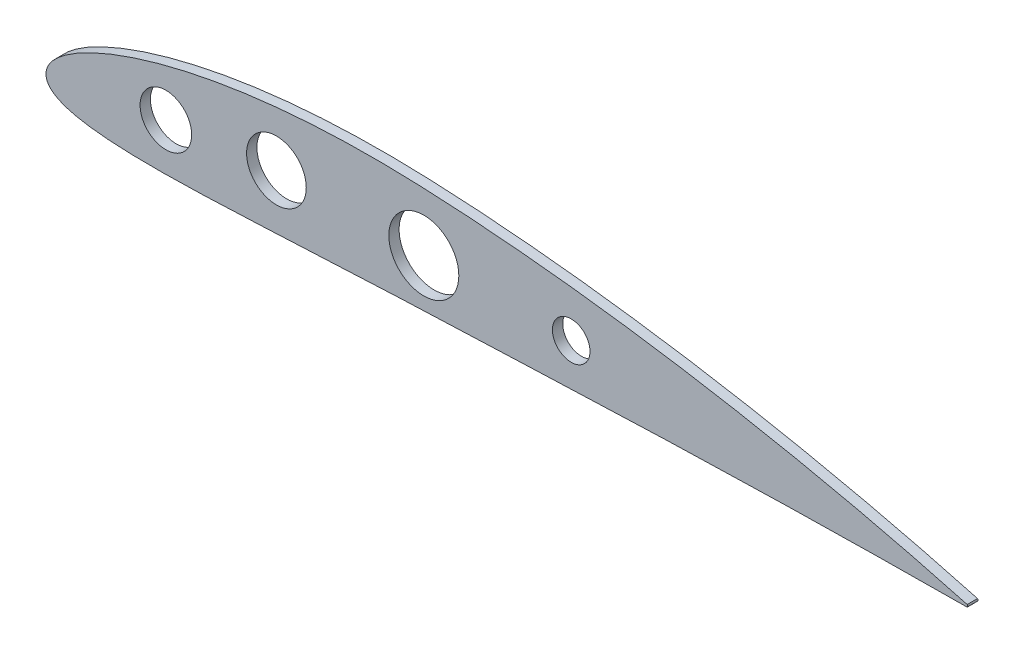
SolidWorks part; units mm, degrees
material "Фанера"
ref_plane "Front Plane" through (0, 0, 0) normal (0, 0, 1) x (1, 0, 0)
ref_plane "Top Plane" through (0, 0, 0) normal (0, 1, 0) x (1, 0, 0)
ref_plane "Right Plane" through (0, 0, 0) normal (1, 0, 0) x (0, 0, -1)
curve "Кривая5"
  spline degree 3 poles (0.048, 0.6214, 0) (0.0227, 0.3735, 0) (-0.0278, -0.1225, 0) (0.078, -0.8844, 0) (0.3497, -1.6388, 0) (0.8143, -2.3651, 0) (1.4635, -3.0393, 0) (2.291, -3.661, 0) (3.3059, -4.2358, 0) (4.5353, -4.7737, 0) (6.0297, -5.2822, 0) (7.869, -5.7653, 0) (10.1688, -6.2217, 0) (13.0754, -6.6396, 0) (16.7281, -6.993, 0) (21.19, -7.2473, 0) (26.4, -7.3766, 0) (32.1974, -7.3763, 0) (38.3978, -7.2614, 0) (44.8576, -7.0566, 0) (51.4865, -6.7865, 0) (58.231, -6.4723, 0) (65.0521, -6.1329, 0) (71.9108, -5.784, 0) (78.7714, -5.4397, 0) (85.6105, -5.111, 0) (92.4321, -4.805, 0) (99.255, -4.532, 0) (106.0974, -4.2783, 0) (112.9692, -4.0031, 0) (119.8644, -3.7232, 0) (126.7739, -3.4401, 0) (133.6816, -3.1587, 0) (140.5819, -2.8824, 0) (147.472, -2.6139, 0) (154.3526, -2.3556, 0) (161.225, -2.1094, 0) (168.0909, -1.8766, 0) (174.9516, -1.6586, 0) (181.8086, -1.4564, 0) (188.6632, -1.2704, 0) (195.5166, -1.1011, 0) (202.3695, -0.9486, 0) (209.2212, -0.8129, 0) (216.0668, -0.6936, 0) (222.8864, -0.5903, 0) (229.6176, -0.5029, 0) (236.0874, -0.4315, 0) (241.9808, -0.3765, 0) (246.559, -0.3395, 0) (249.1205, -0.3213, 0) (250, -0.315, 0) knots 0 0 0 0 0.002941 0.005884 0.009016 0.012365 0.016008 0.020037 0.024574 0.029784 0.035897 0.04324 0.052276 0.063635 0.077983 0.095698 0.11652 0.139661 0.164312 0.189919 0.216157 0.242838 0.269834 0.296993 0.324123 0.351139 0.378036 0.404946 0.431961 0.459078 0.486347 0.513641 0.540929 0.568176 0.59538 0.622543 0.649673 0.676775 0.703855 0.730919 0.757971 0.785018 0.812062 0.839103 0.866132 0.893099 0.919831 0.94581 0.969681 0.98959 1 1 1 1
curve "Кривая6"
  spline degree 3 poles (250, 0.315, 0) (249.1557, 0.545, 0) (246.7202, 1.2085, 0) (242.3913, 2.3583, 0) (236.8498, 3.7876, 0) (230.7799, 5.298, 0) (224.4559, 6.8129, 0) (218.0305, 8.2916, 0) (211.5624, 9.7197, 0) (205.0724, 11.0924, 0) (198.568, 12.4079, 0) (192.0524, 13.6653, 0) (185.5276, 14.8641, 0) (178.9953, 16.0034, 0) (172.4571, 17.0824, 0) (165.9143, 18.0998, 0) (159.3687, 19.0545, 0) (152.8218, 19.9449, 0) (146.2754, 20.7693, 0) (139.7314, 21.5257, 0) (133.1918, 22.212, 0) (126.6587, 22.8257, 0) (120.1368, 23.364, 0) (113.6286, 23.8247, 0) (107.1527, 24.2002, 0) (100.7411, 24.4984, 0) (94.4118, 24.6866, 0) (88.1559, 24.7401, 0) (81.949, 24.6588, 0) (75.7805, 24.441, 0) (69.6537, 24.0819, 0) (63.5754, 23.578, 0) (57.5552, 22.9249, 0) (51.6058, 22.1191, 0) (45.7444, 21.1566, 0) (39.9959, 20.0354, 0) (34.3979, 18.7563, 0) (29.0104, 17.3276, 0) (23.9258, 15.7719, 0) (19.2707, 14.1343, 0) (15.1791, 12.4833, 0) (11.7405, 10.8956, 0) (8.9594, 9.4296, 0) (6.7609, 8.1086, 0) (5.0337, 6.9246, 0) (3.6717, 5.8542, 0) (2.5921, 4.8713, 0) (1.7382, 3.9526, 0) (1.0699, 3.0809, 0) (0.5716, 2.2416, 0) (0.2158, 1.4308, 0) (0.1023, 0.8832, 0) (0.048, 0.6214, 0) knots 0 0 0 0 0.010162 0.029313 0.052012 0.076619 0.101948 0.127526 0.153184 0.178868 0.204558 0.230246 0.255926 0.281594 0.307246 0.332878 0.358485 0.384061 0.409603 0.435104 0.460559 0.485959 0.511303 0.536552 0.561723 0.586629 0.611085 0.635251 0.659272 0.683164 0.706922 0.730536 0.753983 0.777235 0.800246 0.822951 0.845237 0.866916 0.887662 0.906968 0.924203 0.938879 0.950932 0.960693 0.968647 0.975233 0.980795 0.985584 0.989782 0.993521 0.996902 1 1 1 1
sketch "Эскиз1" plane through (0, 0, 0) normal (0, 0, 1) x (1, 0, 0)
  line L0 (250.1305, 0) -> (250.1305, 54.8427) construction
  line L1 (0, 0) -> (0, 70.5199) construction
  line L2 (0, 0) -> (253.0634, 0) construction
  line L3 (62.5326, 62.6361) -> (62.5326, -41.5636) construction
  line L4 (142.5326, 67.9319) -> (142.5326, -57.0034) construction
  line L5 (175.0913, 63.8571) -> (175.0913, -32.3947) construction
  line L6 (32.5326, -14.3434) -> (32.5326, 29.5903) construction
  arc A0 (250, 0.315) -> (250, -0.315) centre (249.685, 0) cw
  circle A1 centre (62.5326, 8.5962) radius 8.1
  circle A2 centre (142.5326, 8.5962) radius 5.1
  circle A3 centre (32.5326, 5.4481) radius 7
  circle A5 centre (102.5326, 8.5962) radius 9.5
  spline S0 degree 3 poles (-1998.9862, 52.2873) (51.3697, 19.9849) (-1.4299, 9.9734) (0.078, -0.8844) (0.3497, -1.6388) (0.8143, -2.3651) (1.4635, -3.0393) (2.291, -3.661) (3.3059, -4.2358) (4.5353, -4.7737) (6.0297, -5.2822) (7.869, -5.7653) (10.1688, -6.2217) (13.0754, -6.6396) (16.7281, -6.993) (21.19, -7.2473) (26.4, -7.3766) (32.1974, -7.3763) (38.3978, -7.2614) (44.8576, -7.0566) (51.4865, -6.7865) (58.231, -6.4723) (65.0521, -6.1329) (71.9108, -5.784) (78.7714, -5.4397) (85.6105, -5.111) (92.4321, -4.805) (99.255, -4.532) (106.0974, -4.2783) (112.9692, -4.0031) (119.8644, -3.7232) (126.7739, -3.4401) (133.6816, -3.1587) (140.5819, -2.8824) (147.472, -2.6139) (154.3526, -2.3556) (161.225, -2.1094) (168.0909, -1.8766) (174.9516, -1.6586) (181.8086, -1.4564) (188.6632, -1.2704) (195.5166, -1.1011) (202.3695, -0.9486) (211.4992, -0.7677) (220.6031, -0.6199) (229.6176, -0.5029) (236.0874, -0.4315) (241.9808, -0.3765) (412.2827, 0.9993) (580.6451, -8.1221) (733.0822, 1918.4656) knots -0.119467 -0.119467 -0.119467 -0.119467 0.002941 0.005884 0.009016 0.012365 0.016008 0.020037 0.024574 0.029784 0.035897 0.04324 0.052276 0.063635 0.077983 0.095698 0.11652 0.139661 0.164312 0.189919 0.216157 0.242838 0.269834 0.296993 0.324123 0.351139 0.378036 0.404946 0.431961 0.459078 0.486347 0.513641 0.540929 0.568176 0.59538 0.622543 0.649673 0.676775 0.703855 0.730919 0.757971 0.785018 0.812062 0.839103 0.893099 0.919831 0.94581 0.969681 0.98959 2.9616 2.9616 2.9616 2.9616 only from (0.048, 0.6214) to (250, -0.315) construction
  spline S1 degree 3 poles (1021.8633, 1838.7787) (414.3615, -64.7736) (332.0293, -21.4512) (242.3913, 2.3583) (236.8498, 3.7876) (230.7799, 5.298) (224.4559, 6.8129) (218.0305, 8.2916) (211.5624, 9.7197) (205.0724, 11.0924) (198.568, 12.4079) (192.0524, 13.6653) (185.5276, 14.8641) (178.9953, 16.0034) (172.4571, 17.0824) (165.9143, 18.0998) (159.3687, 19.0545) (152.8218, 19.9449) (146.2754, 20.7693) (139.7314, 21.5257) (133.1918, 22.212) (126.6587, 22.8257) (120.1368, 23.364) (113.6286, 23.8247) (107.1527, 24.2002) (100.7411, 24.4984) (94.4118, 24.6866) (88.1559, 24.7401) (81.949, 24.6588) (75.7805, 24.441) (69.6537, 24.0819) (63.5754, 23.578) (57.5552, 22.9249) (51.6058, 22.1191) (45.7444, 21.1566) (39.9959, 20.0354) (34.3979, 18.7563) (29.0104, 17.3276) (23.9258, 15.7719) (19.2707, 14.1343) (15.1791, 12.4833) (11.7405, 10.8956) (8.9594, 9.4296) (6.7609, 8.1086) (5.0337, 6.9246) (3.6717, 5.8542) (2.5921, 4.8713) (1.7382, 3.9526) (1.0699, 3.0809) (0.5716, 2.2416) (-4.3308, -8.9285) (41.0506, -34.7699) (-1925.2597, 540.0689) knots -1.025 -1.025 -1.025 -1.025 0.010162 0.029313 0.052012 0.076619 0.101948 0.127526 0.153184 0.178868 0.204558 0.230246 0.255926 0.281594 0.307246 0.332878 0.358485 0.384061 0.409603 0.435104 0.460559 0.485959 0.511303 0.536552 0.561723 0.586629 0.611085 0.635251 0.659272 0.683164 0.706922 0.730536 0.753983 0.777235 0.800246 0.822951 0.845237 0.866916 0.887662 0.906968 0.924203 0.938879 0.950932 0.960693 0.968647 0.975233 0.980795 0.985584 0.989782 0.993521 0.996902 1.130551 1.130551 1.130551 1.130551 only from (250, 0.315) to (0.048, 0.6214) construction
  spline S2 degree 3 poles (0.048, 0.6214) (0.0227, 0.3735) (-0.0278, -0.1225) (0.078, -0.8844) (0.3497, -1.6388) (0.8143, -2.3651) (1.4635, -3.0393) (2.291, -3.661) (3.3059, -4.2358) (4.5353, -4.7737) (6.0297, -5.2822) (7.869, -5.7653) (10.1688, -6.2217) (13.0754, -6.6396) (16.7281, -6.993) (21.19, -7.2473) (26.4, -7.3766) (32.1974, -7.3763) (38.3978, -7.2614) (44.8576, -7.0566) (51.4865, -6.7865) (58.231, -6.4723) (65.0521, -6.1329) (71.9108, -5.784) (78.7714, -5.4397) (85.6105, -5.111) (92.4321, -4.805) (99.255, -4.532) (106.0974, -4.2783) (112.9692, -4.0031) (119.8644, -3.7232) (126.7739, -3.4401) (133.6816, -3.1587) (140.5819, -2.8824) (147.472, -2.6139) (154.3526, -2.3556) (161.225, -2.1094) (168.0909, -1.8766) (174.9516, -1.6586) (181.8086, -1.4564) (188.6632, -1.2704) (195.5166, -1.1011) (202.3695, -0.9486) (211.4992, -0.7677) (220.6031, -0.6199) (229.6176, -0.5029) (236.0874, -0.4315) (241.9808, -0.3765) (246.559, -0.3395) (249.1205, -0.3213) (250, -0.315) knots 0 0 0 0 0.002941 0.005884 0.009016 0.012365 0.016008 0.020037 0.024574 0.029784 0.035897 0.04324 0.052276 0.063635 0.077983 0.095698 0.11652 0.139661 0.164312 0.189919 0.216157 0.242838 0.269834 0.296993 0.324123 0.351139 0.378036 0.404946 0.431961 0.459078 0.486347 0.513641 0.540929 0.568176 0.59538 0.622543 0.649673 0.676775 0.703855 0.730919 0.757971 0.785018 0.812062 0.839103 0.893099 0.919831 0.94581 0.969681 0.98959 1 1 1 1
  spline S3 degree 3 poles (250, 0.315) (249.1557, 0.545) (246.7202, 1.2085) (242.3913, 2.3583) (236.8498, 3.7876) (230.7799, 5.298) (224.4559, 6.8129) (218.0305, 8.2916) (211.5624, 9.7197) (205.0724, 11.0924) (198.568, 12.4079) (192.0524, 13.6653) (185.5276, 14.8641) (178.9953, 16.0034) (172.4571, 17.0824) (165.9143, 18.0998) (159.3687, 19.0545) (152.8218, 19.9449) (146.2754, 20.7693) (139.7314, 21.5257) (133.1918, 22.212) (126.6587, 22.8257) (120.1368, 23.364) (113.6286, 23.8247) (107.1527, 24.2002) (100.7411, 24.4984) (94.4118, 24.6866) (88.1559, 24.7401) (81.949, 24.6588) (75.7805, 24.441) (69.6537, 24.0819) (63.5754, 23.578) (57.5552, 22.9249) (51.6058, 22.1191) (45.7444, 21.1566) (39.9959, 20.0354) (34.3979, 18.7563) (29.0104, 17.3276) (23.9258, 15.7719) (19.2707, 14.1343) (15.1791, 12.4833) (11.7405, 10.8956) (8.9594, 9.4296) (6.7609, 8.1086) (5.0337, 6.9246) (3.6717, 5.8542) (2.5921, 4.8713) (1.7382, 3.9526) (1.0699, 3.0809) (0.5716, 2.2416) (0.2158, 1.4308) (0.1023, 0.8832) (0.048, 0.6214) knots 0 0 0 0 0.010162 0.029313 0.052012 0.076619 0.101948 0.127526 0.153184 0.178868 0.204558 0.230246 0.255926 0.281594 0.307246 0.332878 0.358485 0.384061 0.409603 0.435104 0.460559 0.485959 0.511303 0.536552 0.561723 0.586629 0.611085 0.635251 0.659272 0.683164 0.706922 0.730536 0.753983 0.777235 0.800246 0.822951 0.845237 0.866916 0.887662 0.906968 0.924203 0.938879 0.950932 0.960693 0.968647 0.975233 0.980795 0.985584 0.989782 0.993521 0.996902 1 1 1 1
  point P22 (62.5326, 23.4501)
  point P23 (62.5326, -6.2577)
  point P26 (32.5326, 18.2506)
  point P27 (32.5326, -7.3543)
  dimension "D3" = 16.2
  dimension "D8" = 14
  dimension "D10" = 10.2
  dimension "D9" = 19
  dimension "D1" = 250.1305
  dimension "D2" = 62.5326
  dimension "D4" = 80
  dimension "D5" = 75.0391
  dimension "D6" = 29.7079
  dimension "D7" = 14.8539
  dimension "D11" = 40
  dimension "D12" = 30
  dimension "D13" = 25.6049
  dimension "D14" = 12.8025
extrude "Бобышка-Вытянуть1" add sketch "Эскиз1" along normal mid plane 2.8
equation "\"D2@Эскиз1\"=\"D1@Эскиз1\"/4"
equation "\"D7@Эскиз1\"=\"D6@Эскиз1\"/2"
equation "\"D5@Эскиз1\"=\"D1@Эскиз1\"*0.3"
equation "\"D14@Эскиз1\"=\"D13@Эскиз1\"/2"
